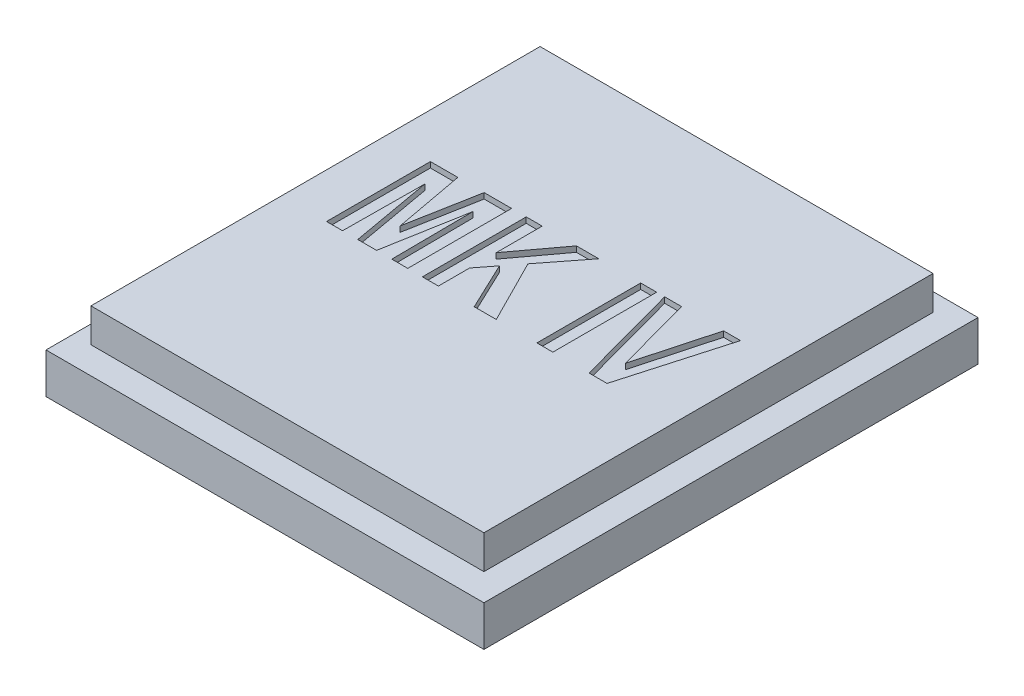
SolidWorks part; units mm, degrees
ref_plane "Спереди" through (0, 0, 0) normal (0, 0, 1) x (1, 0, 0)
ref_plane "Сверху" through (0, 0, 0) normal (0, 1, 0) x (1, 0, 0)
ref_plane "Справа" through (0, 0, 0) normal (1, 0, 0) x (0, 0, -1)
sketch "Sketch1" plane through (0, 0, 0) normal (0, 1, 0) x (1, 0, 0)
  line L1 (13.9, -14.9) -> (-13.9, -14.9)
  line L2 (13.9, -14.9) -> (13.9, 14.9)
  line L3 (13.9, 14.9) -> (-13.9, 14.9)
  line L4 (-13.9, -14.9) -> (-13.9, 14.9)
  line L5 (13.9, -14.9) -> (-13.9, 14.9) construction
  line L6 (13.9, 14.9) -> (-13.9, -14.9) construction
  point P0 (0, 0)
  dimension "D1" = 27.8
  dimension "D2" = 29.8
extrude "Boss-Extrude1" add sketch "Sketch1" along normal blind 4
sketch "Sketch2" plane through (0, 4, 0) normal (0, 1, 0) x (1, 0, 0)
  line L0 (-1.1, 14.9) -> (-1.1, -14.9) construction
  line L1 (13.9, 14.9) -> (-13.9, 14.9) construction
  line L2 (-13.9, -14.9) -> (13.9, -14.9) construction
  line L3 (-13.9, 3.1) -> (13.9, 3.1) construction
  line L4 (-13.9, 14.9) -> (-13.9, -14.9) construction
  line L5 (13.9, -14.9) -> (13.9, 14.9) construction
  line L7 (16.4, -16.9) -> (-18.6, -16.9)
  line L8 (16.4, -16.9) -> (16.4, 23.1)
  line L9 (16.4, 23.1) -> (-18.6, 23.1)
  line L10 (-18.6, -16.9) -> (-18.6, 23.1)
  line L11 (16.4, -16.9) -> (-18.6, 23.1) construction
  line L12 (16.4, 23.1) -> (-18.6, -16.9) construction
  point P12 (-1.1, 3.1)
  dimension "D1" = 35
  dimension "D2" = 40
  dimension "D3" = 18
  dimension "D4" = 15
extrude "Boss-Extrude2" add sketch "Sketch2" along normal blind 3
chamfer "Chamfer1" distance 0.4 angle 70 4 edges at (0, 0, 14.9) (13.9, 0, 0) (0, 0, -14.9) (-13.9, 0, 0)
sketch "Sketch3" plane through (0, 7, 0) normal (0, 1, 0) x (1, 0, 0)
  line L0 (-18.6, 0.1) -> (16.4, 0.1) construction
  line L1 (-18.6, 23.1) -> (-18.6, -16.9) construction
  line L2 (16.4, -16.9) -> (16.4, 23.1) construction
  line L3 (-18.6, -16.9) -> (16.4, -16.9) construction
  text T0 "<b>MK IV</b>" font "Arial" height in points 36
  dimension "D1" = 17
sketch "Sketch4" plane through (0, 0, 0) normal (0, -1, 0) x (1, 0, 0)
  line L0 (-18.6, 16.9) -> (16.4, 16.9) construction
  line L1 (-20.6, 18.9) -> (18.4, 18.9)
  line L2 (-20.6, 18.9) -> (-20.6, -25.1)
  line L3 (-20.6, -25.1) -> (18.4, -25.1)
  line L4 (18.4, 18.9) -> (18.4, -25.1)
  line L5 (-20.6, 18.9) -> (18.4, -25.1) construction
  line L6 (-20.6, -25.1) -> (18.4, 18.9) construction
  line L7 (-16.6, 15.4) -> (14.4, 15.4)
  line L8 (-16.6, 15.4) -> (-16.6, -21.6)
  line L9 (-16.6, -21.6) -> (14.4, -21.6)
  line L10 (14.4, 15.4) -> (14.4, -21.6)
  line L11 (-16.6, 15.4) -> (14.4, -21.6) construction
  line L12 (-16.6, -21.6) -> (14.4, 15.4) construction
  line L13 (16.4, 16.9) -> (16.4, -23.1) construction
  line L14 (16.4, -23.1) -> (-18.6, -23.1) construction
  line L15 (-18.6, -23.1) -> (-18.6, 16.9) construction
  point P0 (-1.1, -3.1)
  point P5 (-1.1, -3.1)
  dimension "D1" = 2
  dimension "D2" = 1.5
  dimension "D3" = 2
  dimension "D4" = 2
  dimension "D5" = 2
  dimension "D6" = 1.5
  dimension "D7" = 2
extrude "Boss-Extrude4" add sketch "Sketch4" against normal offset from surface (3.6 mm away) 0.4 up to face at (-1.1, 4, -3.1)
extrude "Cut-Extrude1" cut sketch "Sketch3" against normal blind 0.5
